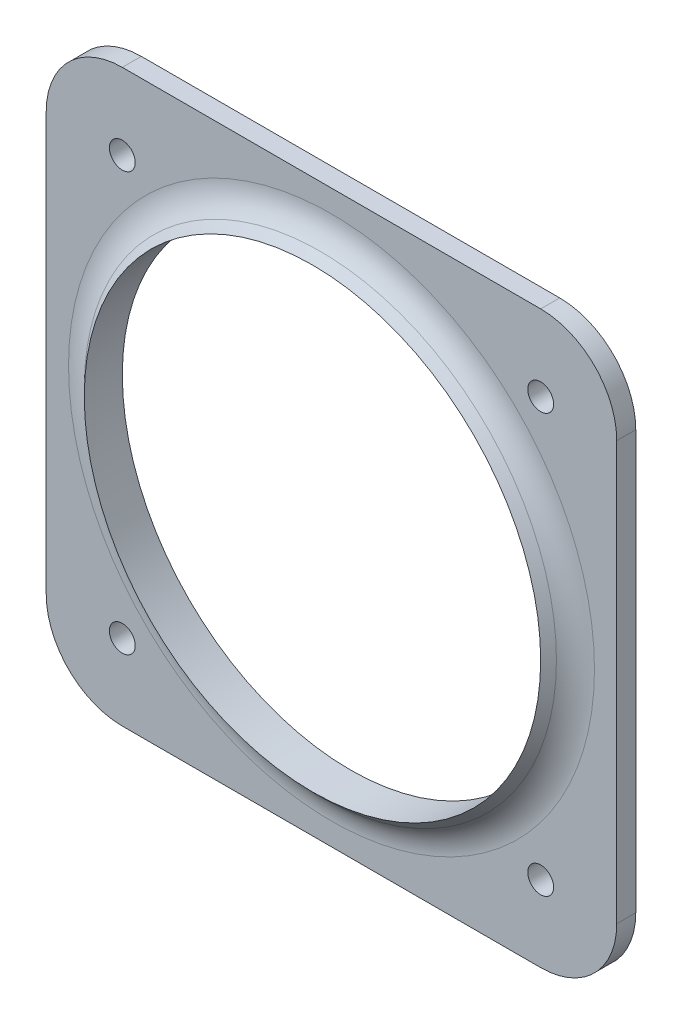
SolidWorks part; units mm, degrees
ref_plane "Front Plane" through (0, 0, 0) normal (0, 0, 1) x (1, 0, 0)
ref_plane "Top Plane" through (0, 0, 0) normal (0, 1, 0) x (1, 0, 0)
ref_plane "Right Plane" through (0, 0, 0) normal (1, 0, 0) x (0, 0, -1)
sketch "Sketch1" plane through (0, 0, 0) normal (0, 0, 1) x (1, 0, 0)
  line L1 (47.625, -47.625) -> (-47.625, -47.625)
  line L2 (47.625, -47.625) -> (47.625, 47.625)
  line L3 (47.625, 47.625) -> (-47.625, 47.625)
  line L4 (-47.625, -47.625) -> (-47.625, 47.625)
  line L5 (47.625, -47.625) -> (-47.625, 47.625) construction
  line L6 (47.625, 47.625) -> (-47.625, -47.625) construction
  circle A0 centre (0, 0) radius 38.1
  point P0 (0, 0)
  dimension "D2" = 76.2
  dimension "D1" = 95.25
extrude "Boss-Extrude1" add sketch "Sketch1" along normal blind 3.175
sketch "Sketch2" plane through (0, 0, 0) normal (0, 1, 0) x (1, 0, 0)
  line L0 (38.1, -3.175) -> (38.1, -6.35)
  line L1 (38.1, -6.35) -> (41.275, -3.175)
  line L2 (41.275, -3.175) -> (38.1, -3.175)
  line L3 (0, -1000) -> (0, 49000) construction
  dimension "D1" = 3.175
  dimension "D2" = 45
revolve "Revolve1" add sketch "Sketch2" angle 360 about L3
fillet "Fillet1" radius 6.35 1 edges at (41.275, 0, 3.175)
sketch "Sketch4" plane through (0, 0, 3.175) normal (0, 0, 1) x (1, 0, 0)
  line L1 (34.925, -34.925) -> (-34.925, -34.925) construction
  line L2 (34.925, -34.925) -> (34.925, 34.925) construction
  line L3 (34.925, 34.925) -> (-34.925, 34.925) construction
  line L4 (-34.925, -34.925) -> (-34.925, 34.925) construction
  line L5 (34.925, -34.925) -> (-34.925, 34.925) construction
  line L6 (34.925, 34.925) -> (-34.925, -34.925) construction
  circle A0 centre (-34.925, 34.925) radius 2.159
  circle A1 centre (34.925, 34.925) radius 2.159
  circle A2 centre (34.925, -34.925) radius 2.159
  circle A3 centre (-34.925, -34.925) radius 2.159
  point P0 (0, 0)
  dimension "D1" = 4.318
  dimension "D2" = 69.85
extrude "Cut-Extrude1" cut sketch "Sketch4" against normal through all
fillet "Fillet2" radius 12.7 4 edges at (-47.625, 47.625, 1.5875) (47.625, 47.625, 1.5875) (47.625, -47.625, 1.5875) (-47.625, -47.625, 1.5875)
